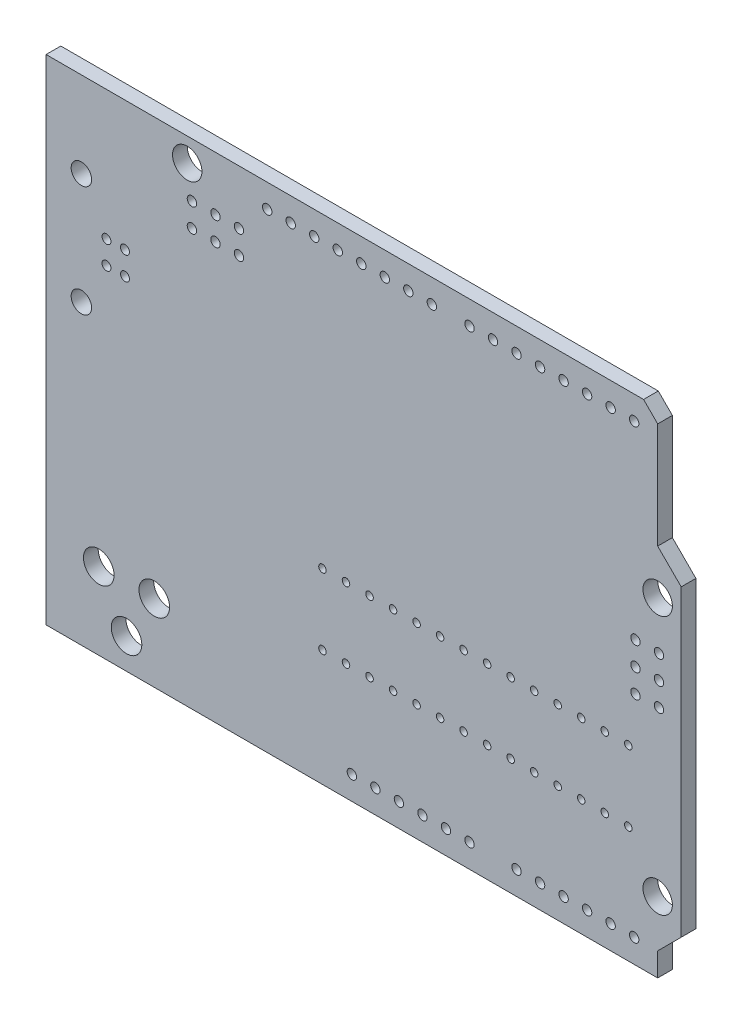
SolidWorks part; units mm, degrees
ref_plane "Front" through (0, 0, 0) normal (0, 0, 1) x (1, 0, 0)
ref_plane "Top" through (0, 0, 0) normal (0, 1, 0) x (1, 0, 0)
ref_plane "Right" through (0, 0, 0) normal (1, 0, 0) x (0, 0, -1)
sketch "Sketch1" plane through (0, 0, 0) normal (0, 0, 1) x (1, 0, 0)
  line L0 (-34.2899, 0) -> (34.2899, 0) construction
  line L1 (0, 0) -> (0, 7.605) construction
  line L2 (31.7499, 13.716) -> (31.7499, 25.146) construction
  line L3 (-34.2899, -26.67) -> (-34.2899, 26.67) construction
  line L4 (-34.2899, -26.67) -> (31.7499, -26.67) construction
  line L5 (31.7499, -26.67) -> (31.7499, -24.13) construction
  line L6 (31.7499, -24.13) -> (34.2899, -21.59) construction
  line L7 (34.2899, -21.59) -> (34.2899, 11.176) construction
  line L8 (31.7499, 13.716) -> (34.2899, 11.176) construction
  line L9 (30.2259, 26.67) -> (31.7499, 25.146) construction
  line L10 (-34.2899, 26.67) -> (30.2259, 26.67) construction
  arc A0 (-21.12, -24.13) -> (-19.5201, -24.13) centre (-20.3201, -24.13) ccw construction
  arc A1 (-19.5201, -24.13) -> (-21.12, -24.13) centre (-20.3201, -24.13) ccw construction
  arc A2 (-19.85, 24.13) -> (-18.2501, 24.13) centre (-19.0501, 24.13) ccw construction
  arc A3 (-18.2501, 24.13) -> (-19.85, 24.13) centre (-19.0501, 24.13) ccw construction
  arc A4 (30.95, -19.05) -> (32.5499, -19.05) centre (31.7499, -19.05) ccw construction
  arc A5 (32.5499, -19.05) -> (30.95, -19.05) centre (31.7499, -19.05) ccw construction
  arc A6 (30.95, 8.89) -> (32.5499, 8.89) centre (31.7499, 8.89) ccw construction
  arc A7 (32.5499, 8.89) -> (30.95, 8.89) centre (31.7499, 8.89) ccw construction
  arc A8 (28.3717, -14.097) -> (28.7781, -14.097) centre (28.5749, -14.097) ccw construction
  arc A9 (28.7781, -14.097) -> (28.3717, -14.097) centre (28.5749, -14.097) ccw construction
  arc A10 (25.8317, -14.097) -> (26.2381, -14.097) centre (26.0349, -14.097) ccw construction
  arc A11 (26.2381, -14.097) -> (25.8317, -14.097) centre (26.0349, -14.097) ccw construction
  arc A12 (23.2917, -14.097) -> (23.6981, -14.097) centre (23.4949, -14.097) ccw construction
  arc A13 (23.6981, -14.097) -> (23.2917, -14.097) centre (23.4949, -14.097) ccw construction
  arc A14 (20.7517, -14.097) -> (21.1581, -14.097) centre (20.9549, -14.097) ccw construction
  arc A15 (21.1581, -14.097) -> (20.7517, -14.097) centre (20.9549, -14.097) ccw construction
  arc A16 (18.2117, -14.097) -> (18.6181, -14.097) centre (18.4149, -14.097) ccw construction
  arc A17 (18.6181, -14.097) -> (18.2117, -14.097) centre (18.4149, -14.097) ccw construction
  arc A18 (15.6717, -14.097) -> (16.0781, -14.097) centre (15.8749, -14.097) ccw construction
  arc A19 (16.0781, -14.097) -> (15.6717, -14.097) centre (15.8749, -14.097) ccw construction
  arc A20 (13.1317, -14.097) -> (13.5381, -14.097) centre (13.3349, -14.097) ccw construction
  arc A21 (13.5381, -14.097) -> (13.1317, -14.097) centre (13.3349, -14.097) ccw construction
  arc A22 (10.5917, -14.097) -> (10.9981, -14.097) centre (10.7949, -14.097) ccw construction
  arc A23 (10.9981, -14.097) -> (10.5917, -14.097) centre (10.7949, -14.097) ccw construction
  arc A24 (8.0517, -14.097) -> (8.4581, -14.097) centre (8.2549, -14.097) ccw construction
  arc A25 (8.4581, -14.097) -> (8.0517, -14.097) centre (8.2549, -14.097) ccw construction
  arc A26 (5.5117, -14.097) -> (5.9181, -14.097) centre (5.7149, -14.097) ccw construction
  arc A27 (5.9181, -14.097) -> (5.5117, -14.097) centre (5.7149, -14.097) ccw construction
  arc A28 (2.9717, -14.097) -> (3.3781, -14.097) centre (3.1749, -14.097) ccw construction
  arc A29 (3.3781, -14.097) -> (2.9717, -14.097) centre (3.1749, -14.097) ccw construction
  arc A30 (0.4317, -14.097) -> (0.8381, -14.097) centre (0.6349, -14.097) ccw construction
  arc A31 (0.8381, -14.097) -> (0.4317, -14.097) centre (0.6349, -14.097) ccw construction
  arc A32 (-2.1083, -14.097) -> (-1.7019, -14.097) centre (-1.9051, -14.097) ccw construction
  arc A33 (-1.7019, -14.097) -> (-2.1083, -14.097) centre (-1.9051, -14.097) ccw construction
  arc A34 (-4.6483, -14.097) -> (-4.2419, -14.097) centre (-4.4451, -14.097) ccw construction
  arc A35 (-4.2419, -14.097) -> (-4.6483, -14.097) centre (-4.4451, -14.097) ccw construction
  arc A36 (-4.6483, -6.477) -> (-4.2419, -6.477) centre (-4.4451, -6.477) ccw construction
  arc A37 (-4.2419, -6.477) -> (-4.6483, -6.477) centre (-4.4451, -6.477) ccw construction
  arc A38 (-2.1083, -6.477) -> (-1.7019, -6.477) centre (-1.9051, -6.477) ccw construction
  arc A39 (-1.7019, -6.477) -> (-2.1083, -6.477) centre (-1.9051, -6.477) ccw construction
  arc A40 (0.4317, -6.477) -> (0.8381, -6.477) centre (0.6349, -6.477) ccw construction
  arc A41 (0.8381, -6.477) -> (0.4317, -6.477) centre (0.6349, -6.477) ccw construction
  arc A42 (2.9717, -6.477) -> (3.3781, -6.477) centre (3.1749, -6.477) ccw construction
  arc A43 (3.3781, -6.477) -> (2.9717, -6.477) centre (3.1749, -6.477) ccw construction
  arc A44 (5.5117, -6.477) -> (5.9181, -6.477) centre (5.7149, -6.477) ccw construction
  arc A45 (5.9181, -6.477) -> (5.5117, -6.477) centre (5.7149, -6.477) ccw construction
  arc A46 (8.0517, -6.477) -> (8.4581, -6.477) centre (8.2549, -6.477) ccw construction
  arc A47 (8.4581, -6.477) -> (8.0517, -6.477) centre (8.2549, -6.477) ccw construction
  arc A48 (10.5917, -6.477) -> (10.9981, -6.477) centre (10.7949, -6.477) ccw construction
  arc A49 (10.9981, -6.477) -> (10.5917, -6.477) centre (10.7949, -6.477) ccw construction
  arc A50 (13.1317, -6.477) -> (13.5381, -6.477) centre (13.3349, -6.477) ccw construction
  arc A51 (13.5381, -6.477) -> (13.1317, -6.477) centre (13.3349, -6.477) ccw construction
  arc A52 (15.6717, -6.477) -> (16.0781, -6.477) centre (15.8749, -6.477) ccw construction
  arc A53 (16.0781, -6.477) -> (15.6717, -6.477) centre (15.8749, -6.477) ccw construction
  arc A54 (18.2117, -6.477) -> (18.6181, -6.477) centre (18.4149, -6.477) ccw construction
  arc A55 (18.6181, -6.477) -> (18.2117, -6.477) centre (18.4149, -6.477) ccw construction
  arc A56 (20.7517, -6.477) -> (21.1581, -6.477) centre (20.9549, -6.477) ccw construction
  arc A57 (21.1581, -6.477) -> (20.7517, -6.477) centre (20.9549, -6.477) ccw construction
  arc A58 (23.2917, -6.477) -> (23.6981, -6.477) centre (23.4949, -6.477) ccw construction
  arc A59 (23.6981, -6.477) -> (23.2917, -6.477) centre (23.4949, -6.477) ccw construction
  arc A60 (25.8317, -6.477) -> (26.2381, -6.477) centre (26.0349, -6.477) ccw construction
  arc A61 (26.2381, -6.477) -> (25.8317, -6.477) centre (26.0349, -6.477) ccw construction
  arc A62 (28.3717, -6.477) -> (28.7781, -6.477) centre (28.5749, -6.477) ccw construction
  arc A63 (28.7781, -6.477) -> (28.3717, -6.477) centre (28.5749, -6.477) ccw construction
  arc A64 (-31.0299, 5.43) -> (-29.93, 5.43) centre (-30.4799, 5.43) ccw construction
  arc A65 (-29.93, 5.43) -> (-31.0299, 5.43) centre (-30.4799, 5.43) ccw construction
  arc A66 (-31.0299, 17.43) -> (-29.93, 17.43) centre (-30.4799, 17.43) ccw construction
  arc A67 (-29.93, 17.43) -> (-31.0299, 17.43) centre (-30.4799, 17.43) ccw construction
  arc A68 (-28.0074, 10.1801) -> (-27.5324, 10.1801) centre (-27.7699, 10.1801) ccw construction
  arc A69 (-27.5324, 10.1801) -> (-28.0074, 10.1801) centre (-27.7699, 10.1801) ccw construction
  arc A70 (-28.0074, 12.6799) -> (-27.5324, 12.6799) centre (-27.7699, 12.6799) ccw construction
  arc A71 (-27.5324, 12.6799) -> (-28.0074, 12.6799) centre (-27.7699, 12.6799) ccw construction
  arc A72 (-26.0075, 12.6799) -> (-25.5325, 12.6799) centre (-25.77, 12.6799) ccw construction
  arc A73 (-25.5325, 12.6799) -> (-26.0075, 12.6799) centre (-25.77, 12.6799) ccw construction
  arc A74 (-26.0075, 10.1801) -> (-25.5325, 10.1801) centre (-25.77, 10.1801) ccw construction
  arc A75 (-25.5325, 10.1801) -> (-26.0075, 10.1801) centre (-25.77, 10.1801) ccw construction
  arc A76 (-29.4258, -18.3642) -> (-27.7748, -18.3642) centre (-28.6003, -18.3642) ccw construction
  arc A77 (-27.7748, -18.3642) -> (-29.4258, -18.3642) centre (-28.6003, -18.3642) ccw construction
  arc A78 (-23.4316, -18.3642) -> (-21.7806, -18.3642) centre (-22.6061, -18.3642) ccw construction
  arc A79 (-21.7806, -18.3642) -> (-23.4316, -18.3642) centre (-22.6061, -18.3642) ccw construction
  arc A80 (-26.4286, -23.368) -> (-24.7776, -23.368) centre (-25.6031, -23.368) ccw construction
  arc A81 (-24.7776, -23.368) -> (-26.4286, -23.368) centre (-25.6031, -23.368) ccw construction
  arc A82 (8.7375, -2.54) -> (9.0423, -2.54) centre (8.8899, -2.54) ccw construction
  arc A83 (9.0423, -2.54) -> (8.7375, -2.54) centre (8.8899, -2.54) ccw construction
  arc A84 (3.6575, -2.54) -> (3.9623, -2.54) centre (3.8099, -2.54) ccw construction
  arc A85 (3.9623, -2.54) -> (3.6575, -2.54) centre (3.8099, -2.54) ccw construction
  arc A86 (-20.4725, 3.81) -> (-20.1677, 3.81) centre (-20.3201, 3.81) ccw construction
  arc A87 (-20.1677, 3.81) -> (-20.4725, 3.81) centre (-20.3201, 3.81) ccw construction
  arc A88 (-15.3925, 3.81) -> (-15.0877, 3.81) centre (-15.2401, 3.81) ccw construction
  arc A89 (-15.0877, 3.81) -> (-15.3925, 3.81) centre (-15.2401, 3.81) ccw construction
  arc A90 (11.1759, -24.13) -> (11.6839, -24.13) centre (11.4299, -24.13) ccw construction
  arc A91 (11.6839, -24.13) -> (11.1759, -24.13) centre (11.4299, -24.13) ccw construction
  arc A92 (8.6359, -24.13) -> (9.1439, -24.13) centre (8.8899, -24.13) ccw construction
  arc A93 (9.1439, -24.13) -> (8.6359, -24.13) centre (8.8899, -24.13) ccw construction
  arc A94 (6.0959, -24.13) -> (6.6039, -24.13) centre (6.3499, -24.13) ccw construction
  arc A95 (6.6039, -24.13) -> (6.0959, -24.13) centre (6.3499, -24.13) ccw construction
  arc A96 (3.5559, -24.13) -> (4.0639, -24.13) centre (3.8099, -24.13) ccw construction
  arc A97 (4.0639, -24.13) -> (3.5559, -24.13) centre (3.8099, -24.13) ccw construction
  arc A98 (1.0159, -24.13) -> (1.5239, -24.13) centre (1.2699, -24.13) ccw construction
  arc A99 (1.5239, -24.13) -> (1.0159, -24.13) centre (1.2699, -24.13) ccw construction
  arc A100 (-1.5241, -24.13) -> (-1.0161, -24.13) centre (-1.2701, -24.13) ccw construction
  arc A101 (-1.0161, -24.13) -> (-1.5241, -24.13) centre (-1.2701, -24.13) ccw construction
  arc A102 (11.1759, 24.13) -> (11.6839, 24.13) centre (11.4299, 24.13) ccw construction
  arc A103 (11.6839, 24.13) -> (11.1759, 24.13) centre (11.4299, 24.13) ccw construction
  arc A104 (13.7159, 24.13) -> (14.2239, 24.13) centre (13.9699, 24.13) ccw construction
  arc A105 (14.2239, 24.13) -> (13.7159, 24.13) centre (13.9699, 24.13) ccw construction
  arc A106 (16.2559, 24.13) -> (16.7639, 24.13) centre (16.5099, 24.13) ccw construction
  arc A107 (16.7639, 24.13) -> (16.2559, 24.13) centre (16.5099, 24.13) ccw construction
  arc A108 (18.7959, 24.13) -> (19.3039, 24.13) centre (19.0499, 24.13) ccw construction
  arc A109 (19.3039, 24.13) -> (18.7959, 24.13) centre (19.0499, 24.13) ccw construction
  arc A110 (21.3359, 24.13) -> (21.8439, 24.13) centre (21.5899, 24.13) ccw construction
  arc A111 (21.8439, 24.13) -> (21.3359, 24.13) centre (21.5899, 24.13) ccw construction
  arc A112 (23.8759, 24.13) -> (24.3839, 24.13) centre (24.1299, 24.13) ccw construction
  arc A113 (24.3839, 24.13) -> (23.8759, 24.13) centre (24.1299, 24.13) ccw construction
  arc A114 (26.4159, 24.13) -> (26.9239, 24.13) centre (26.6699, 24.13) ccw construction
  arc A115 (26.9239, 24.13) -> (26.4159, 24.13) centre (26.6699, 24.13) ccw construction
  arc A116 (28.9559, 24.13) -> (29.4639, 24.13) centre (29.2099, 24.13) ccw construction
  arc A117 (29.4639, 24.13) -> (28.9559, 24.13) centre (29.2099, 24.13) ccw construction
  arc A118 (-10.6681, 24.13) -> (-10.1601, 24.13) centre (-10.4141, 24.13) ccw construction
  arc A119 (-10.1601, 24.13) -> (-10.6681, 24.13) centre (-10.4141, 24.13) ccw construction
  arc A120 (-8.1281, 24.13) -> (-7.6201, 24.13) centre (-7.8741, 24.13) ccw construction
  arc A121 (-7.6201, 24.13) -> (-8.1281, 24.13) centre (-7.8741, 24.13) ccw construction
  arc A122 (-5.5881, 24.13) -> (-5.0801, 24.13) centre (-5.3341, 24.13) ccw construction
  arc A123 (-5.0801, 24.13) -> (-5.5881, 24.13) centre (-5.3341, 24.13) ccw construction
  arc A124 (-3.0481, 24.13) -> (-2.5401, 24.13) centre (-2.7941, 24.13) ccw construction
  arc A125 (-2.5401, 24.13) -> (-3.0481, 24.13) centre (-2.7941, 24.13) ccw construction
  arc A126 (-0.5081, 24.13) -> (-0.0001, 24.13) centre (-0.2541, 24.13) ccw construction
  arc A127 (-0.0001, 24.13) -> (-0.5081, 24.13) centre (-0.2541, 24.13) ccw construction
  arc A128 (2.0319, 24.13) -> (2.5399, 24.13) centre (2.2859, 24.13) ccw construction
  arc A129 (2.5399, 24.13) -> (2.0319, 24.13) centre (2.2859, 24.13) ccw construction
  arc A130 (4.5719, 24.13) -> (5.0799, 24.13) centre (4.8259, 24.13) ccw construction
  arc A131 (5.0799, 24.13) -> (4.5719, 24.13) centre (4.8259, 24.13) ccw construction
  arc A132 (7.1119, 24.13) -> (7.6199, 24.13) centre (7.3659, 24.13) ccw construction
  arc A133 (7.6199, 24.13) -> (7.1119, 24.13) centre (7.3659, 24.13) ccw construction
  arc A134 (-18.7961, 18.288) -> (-18.2881, 18.288) centre (-18.5421, 18.288) ccw construction
  arc A135 (-18.2881, 18.288) -> (-18.7961, 18.288) centre (-18.5421, 18.288) ccw construction
  arc A136 (-18.7961, 20.828) -> (-18.2881, 20.828) centre (-18.5421, 20.828) ccw construction
  arc A137 (-18.2881, 20.828) -> (-18.7961, 20.828) centre (-18.5421, 20.828) ccw construction
  arc A138 (-16.2561, 18.288) -> (-15.7481, 18.288) centre (-16.0021, 18.288) ccw construction
  arc A139 (-15.7481, 18.288) -> (-16.2561, 18.288) centre (-16.0021, 18.288) ccw construction
  arc A140 (-16.2561, 20.828) -> (-15.7481, 20.828) centre (-16.0021, 20.828) ccw construction
  arc A141 (-15.7481, 20.828) -> (-16.2561, 20.828) centre (-16.0021, 20.828) ccw construction
  arc A142 (-13.7161, 18.288) -> (-13.2081, 18.288) centre (-13.4621, 18.288) ccw construction
  arc A143 (-13.2081, 18.288) -> (-13.7161, 18.288) centre (-13.4621, 18.288) ccw construction
  arc A144 (-13.7161, 20.828) -> (-13.2081, 20.828) centre (-13.4621, 20.828) ccw construction
  arc A145 (-13.2081, 20.828) -> (-13.7161, 20.828) centre (-13.4621, 20.828) ccw construction
  arc A146 (31.6362, -1.32) -> (32.1442, -1.32) centre (31.8902, -1.32) ccw construction
  arc A147 (32.1442, -1.32) -> (31.6362, -1.32) centre (31.8902, -1.32) ccw construction
  arc A148 (29.0962, -1.32) -> (29.6042, -1.32) centre (29.3502, -1.32) ccw construction
  arc A149 (29.6042, -1.32) -> (29.0962, -1.32) centre (29.3502, -1.32) ccw construction
  arc A150 (31.6362, 1.22) -> (32.1442, 1.22) centre (31.8902, 1.22) ccw construction
  arc A151 (32.1442, 1.22) -> (31.6362, 1.22) centre (31.8902, 1.22) ccw construction
  arc A152 (29.0962, 1.22) -> (29.6042, 1.22) centre (29.3502, 1.22) ccw construction
  arc A153 (29.6042, 1.22) -> (29.0962, 1.22) centre (29.3502, 1.22) ccw construction
  arc A154 (31.6362, 3.76) -> (32.1442, 3.76) centre (31.8902, 3.76) ccw construction
  arc A155 (32.1442, 3.76) -> (31.6362, 3.76) centre (31.8902, 3.76) ccw construction
  arc A156 (29.0962, 3.76) -> (29.6042, 3.76) centre (29.3502, 3.76) ccw construction
  arc A157 (29.6042, 3.76) -> (29.0962, 3.76) centre (29.3502, 3.76) ccw construction
  arc A158 (28.9559, -24.13) -> (29.4639, -24.13) centre (29.2099, -24.13) ccw construction
  arc A159 (29.4639, -24.13) -> (28.9559, -24.13) centre (29.2099, -24.13) ccw construction
  arc A160 (26.4159, -24.13) -> (26.9239, -24.13) centre (26.6699, -24.13) ccw construction
  arc A161 (26.9239, -24.13) -> (26.4159, -24.13) centre (26.6699, -24.13) ccw construction
  arc A162 (23.8759, -24.13) -> (24.3839, -24.13) centre (24.1299, -24.13) ccw construction
  arc A163 (24.3839, -24.13) -> (23.8759, -24.13) centre (24.1299, -24.13) ccw construction
  arc A164 (21.3359, -24.13) -> (21.8439, -24.13) centre (21.5899, -24.13) ccw construction
  arc A165 (21.8439, -24.13) -> (21.3359, -24.13) centre (21.5899, -24.13) ccw construction
  arc A166 (18.7959, -24.13) -> (19.3039, -24.13) centre (19.0499, -24.13) ccw construction
  arc A167 (19.3039, -24.13) -> (18.7959, -24.13) centre (19.0499, -24.13) ccw construction
  arc A168 (16.2559, -24.13) -> (16.7639, -24.13) centre (16.5099, -24.13) ccw construction
  arc A169 (16.7639, -24.13) -> (16.2559, -24.13) centre (16.5099, -24.13) ccw construction
sketch "Sketch2" plane through (0, 0, 0) normal (0, 0, 1) x (1, 0, 0)
  line L0 (-34.2899, 26.67) -> (30.2259, 26.67) construction
  line L1 (-34.2899, -26.67) -> (-34.2899, 26.67) construction
  line L2 (-34.2899, -26.67) -> (31.7499, -26.67) construction
  line L3 (31.7499, -26.67) -> (31.7499, -24.13) construction
  line L4 (31.7499, -24.13) -> (34.2899, -21.59) construction
  line L5 (34.2899, -21.59) -> (34.2899, 11.176) construction
  line L6 (31.7499, 13.716) -> (34.2899, 11.176) construction
  line L7 (31.7499, 13.716) -> (31.7499, 25.146) construction
  line L8 (30.2259, 26.67) -> (31.7499, 25.146) construction
  line L9 (-34.2899, 26.67) -> (30.2259, 26.67)
  line L10 (-34.2899, -26.67) -> (-34.2899, 26.67)
  line L11 (-34.2899, -26.67) -> (31.7499, -26.67)
  line L12 (31.7499, -26.67) -> (31.7499, -24.13)
  line L13 (31.7499, -24.13) -> (34.2899, -21.59)
  line L14 (34.2899, -21.59) -> (34.2899, 11.176)
  line L15 (31.7499, 13.716) -> (34.2899, 11.176)
  line L16 (31.7499, 13.716) -> (31.7499, 25.146)
  line L17 (30.2259, 26.67) -> (31.7499, 25.146)
extrude "Boss-Extrude1" add sketch "Sketch2" against normal blind 1.5875
sketch "Sketch3" plane through (0, 0, 0) normal (0, 0, 1) x (1, 0, 0)
  circle A0 centre (-30.4799, 17.43) radius 1.1049
  circle A1 centre (-30.4799, 5.43) radius 1.1049
  circle A2 centre (-28.6003, -18.3642) radius 1.651
  circle A3 centre (-25.6031, -23.368) radius 1.651
  circle A4 centre (-22.6061, -18.3642) radius 1.651
  circle A5 centre (31.7499, -19.05) radius 1.5875
  circle A6 centre (31.7499, 8.89) radius 1.5875
  circle A7 centre (-19.0501, 24.13) radius 1.5875
  circle A8 centre (-25.77, 12.6799) radius 0.4826
  circle A9 centre (-27.7699, 12.6799) radius 0.4826
  circle A10 centre (-27.7699, 10.1801) radius 0.4826
  circle A11 centre (-25.77, 10.1801) radius 0.4826
  dimension "D1" = 3.175
  dimension "D2" = 3.175
  dimension "D3" = 3.175
  dimension "D4" = 3.302
  dimension "D5" = 3.302
  dimension "D6" = 3.302
  dimension "D7" = 2.2098
  dimension "D8" = 2.2098
  dimension "D9" = 0.9652
  dimension "D10" = 0.9652
  dimension "D11" = 0.9652
  dimension "D12" = 0.9652
extrude "Cut-Extrude1" cut sketch "Sketch3" against normal through all
sketch "Sketch4" plane through (0, 0, 0) normal (0, 0, 1) x (1, 0, 0)
  circle A0 centre (29.2099, 24.13) radius 0.508
  circle A1 centre (26.6699, 24.13) radius 0.508
  circle A2 centre (24.1299, 24.13) radius 0.508
  circle A3 centre (21.5899, 24.13) radius 0.508
  circle A4 centre (19.0499, 24.13) radius 0.508
  circle A5 centre (16.5099, 24.13) radius 0.508
  circle A6 centre (13.9699, 24.13) radius 0.508
  circle A7 centre (11.4299, 24.13) radius 0.508
  circle A8 centre (7.3659, 24.13) radius 0.508
  circle A9 centre (4.8259, 24.13) radius 0.508
  circle A10 centre (2.2859, 24.13) radius 0.508
  circle A11 centre (-0.2541, 24.13) radius 0.508
  circle A12 centre (-2.7941, 24.13) radius 0.508
  circle A13 centre (-5.3341, 24.13) radius 0.508
  circle A14 centre (-7.8741, 24.13) radius 0.508
  circle A15 centre (-10.4141, 24.13) radius 0.508
  circle A16 centre (28.5749, -6.477) radius 0.4064
  circle A17 centre (26.0349, -6.477) radius 0.4064
  circle A18 centre (23.4949, -6.477) radius 0.4064
  circle A19 centre (20.9549, -6.477) radius 0.4064
  circle A20 centre (18.4149, -6.477) radius 0.4064
  circle A21 centre (15.8749, -6.477) radius 0.4064
  circle A22 centre (13.3349, -6.477) radius 0.4064
  circle A23 centre (10.7949, -6.477) radius 0.4064
  circle A24 centre (8.2549, -6.477) radius 0.4064
  circle A25 centre (5.7149, -6.477) radius 0.4064
  circle A26 centre (3.1749, -6.477) radius 0.4064
  circle A27 centre (0.6349, -6.477) radius 0.4064
  circle A28 centre (-1.9051, -6.477) radius 0.4064
  circle A29 centre (-4.4451, -6.477) radius 0.4064
  circle A30 centre (28.5749, -14.097) radius 0.4064
  circle A31 centre (26.0349, -14.097) radius 0.4064
  circle A32 centre (23.4949, -14.097) radius 0.4064
  circle A33 centre (20.9549, -14.097) radius 0.4064
  circle A34 centre (18.4149, -14.097) radius 0.4064
  circle A35 centre (15.8749, -14.097) radius 0.4064
  circle A36 centre (13.3349, -14.097) radius 0.4064
  circle A37 centre (10.7949, -14.097) radius 0.4064
  circle A38 centre (8.2549, -14.097) radius 0.4064
  circle A39 centre (5.7149, -14.097) radius 0.4064
  circle A40 centre (3.1749, -14.097) radius 0.4064
  circle A41 centre (0.6349, -14.097) radius 0.4064
  circle A42 centre (-1.9051, -14.097) radius 0.4064
  circle A43 centre (-4.4451, -14.097) radius 0.4064
  circle A44 centre (29.2099, -24.13) radius 0.508
  circle A45 centre (11.4299, -24.13) radius 0.508
  circle A46 centre (26.6699, -24.13) radius 0.508
  circle A47 centre (8.8899, -24.13) radius 0.508
  circle A48 centre (24.1299, -24.13) radius 0.508
  circle A49 centre (6.3499, -24.13) radius 0.508
  circle A50 centre (21.5899, -24.13) radius 0.508
  circle A51 centre (3.8099, -24.13) radius 0.508
  circle A52 centre (19.0499, -24.13) radius 0.508
  circle A53 centre (1.2699, -24.13) radius 0.508
  circle A54 centre (16.5099, -24.13) radius 0.508
  circle A55 centre (-1.2701, -24.13) radius 0.508
  circle A56 centre (-13.4621, 20.828) radius 0.508
  circle A57 centre (-13.4621, 18.288) radius 0.508
  circle A58 centre (-16.0021, 18.288) radius 0.508
  circle A59 centre (-16.0021, 20.828) radius 0.508
  circle A60 centre (-18.5421, 18.288) radius 0.508
  circle A61 centre (-18.5421, 20.828) radius 0.508
  circle A62 centre (31.8902, -1.32) radius 0.508
  circle A63 centre (29.3502, -1.32) radius 0.508
  circle A64 centre (29.3502, 1.22) radius 0.508
  circle A65 centre (31.8902, 1.22) radius 0.508
  circle A66 centre (29.3502, 3.76) radius 0.508
  circle A67 centre (31.8902, 3.76) radius 0.508
  dimension "D1" = 1.016
  dimension "D3" = 1.016
  dimension "D5" = 0.8128
  dimension "D7" = 0.8128
  dimension "D9" = 1.016
  dimension "D10" = 1.016
  dimension "D12" = 1.016
  dimension "D13" = 1.016
  dimension "D15" = 1.016
  dimension "D16" = 1.016
  dimension "D2" = 8
  dimension "D4" = 8
  dimension "D6" = 14
  dimension "D8" = 14
  dimension "D11" = 6
  dimension "D14" = 3
  dimension "D17" = 3
extrude "Cut-Extrude2" cut sketch "Sketch4" against normal through all
